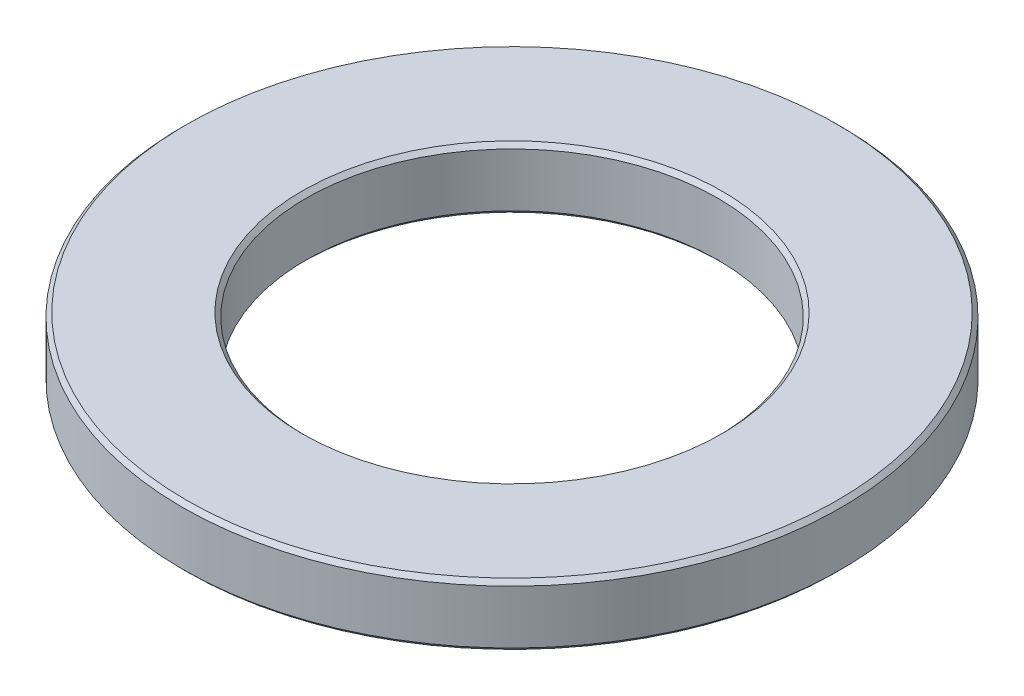
SolidWorks part; units mm, degrees
material "6061-T6 (SS)"
ref_plane "Front Plane" through (0, 0, 0) normal (0, 0, 1) x (1, 0, 0)
ref_plane "Top Plane" through (0, 0, 0) normal (0, 1, 0) x (1, 0, 0)
ref_plane "Right Plane" through (0, 0, 0) normal (1, 0, 0) x (0, 0, -1)
sketch "ProfileS" plane through (0, 0, 0) normal (0, 1, 0) x (1, 0, 0)
  circle A0 centre (0, 0) radius 5
  circle A1 centre (0, 0) radius 8
  dimension "InnerDia" = 10
  dimension "RefDia" = 16
  dimension "DiaControl" = 3
extrude "Profile" add sketch "ProfileS" along normal blind 1.5
chamfer "OuterC" distance 0.1 angle 45 2 edges at (0, 0, 8) (0, 1.5, 8)
chamfer "InnerC" distance 0.1 2 edges at (0, 0, 5) (0, 1.5, 5)
